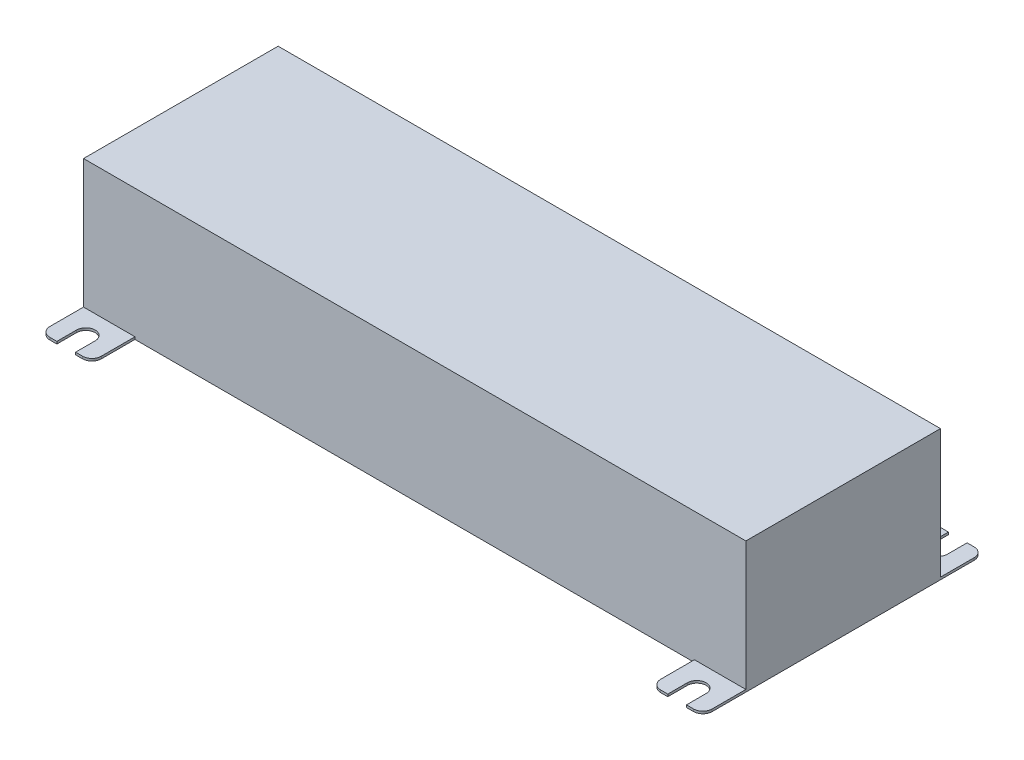
SolidWorks part; units mm, degrees
material "201.0-T43, per stampo in conchiglia (SS)"
ref_plane "Front Plane" through (0, 0, 0) normal (0, 0, 1) x (1, 0, 0)
ref_plane "Top Plane" through (0, 0, 0) normal (0, 1, 0) x (1, 0, 0)
ref_plane "Right Plane" through (0, 0, 0) normal (1, 0, 0) x (0, 0, -1)
sketch "Schizzo1" plane through (0, 0, 0) normal (0, 1, 0) x (1, 0, 0)
  line L0 (-70.8, 20.8) -> (70.8, -20.8) construction
  line L1 (-70.8, 20.8) -> (70.8, 20.8)
  line L2 (-70.8, 20.8) -> (-70.8, -20.8)
  line L3 (-70.8, -20.8) -> (70.8, -20.8)
  line L4 (70.8, 20.8) -> (70.8, -20.8)
  line L5 (-70.8, 0) -> (70.8, 0) construction
  point P4 (0, 0)
  dimension "D1" = 141.6
  dimension "D2" = 41.6
extrude "Estrusione-Estrusione1" add sketch "Schizzo1" along normal blind 28
sketch "Schizzo2" plane through (0, 0, 0) normal (0, 1, 0) x (1, 0, 0)
  line L0 (-70.8, 20.8) -> (-70.8, 28)
  line L1 (-68.8, 30) -> (-67.3, 30)
  line L2 (-67.3, 30) -> (-67.3, 25.8)
  line L3 (-59.8, 28) -> (-59.8, 20.8)
  line L4 (70.8, 20.8) -> (-70.8, 20.8) construction
  line L5 (-59.8, 20.8) -> (-70.8, 20.8)
  line L6 (-63.3, 25.8) -> (-63.3, 30)
  line L7 (-63.3, 30) -> (-61.8, 30)
  line L8 (-65.3, 20.8) -> (-65.3, 31.1814) construction
  line L9 (-70.8, 0) -> (0, 0) construction
  line L10 (-63.3, -30) -> (-61.8, -30)
  line L11 (-63.3, -25.8) -> (-63.3, -30)
  line L12 (-67.3, -30) -> (-67.3, -25.8)
  line L13 (-68.8, -30) -> (-67.3, -30)
  line L14 (-70.8, -20.8) -> (-70.8, -28)
  line L15 (-59.8, -20.8) -> (-70.8, -20.8)
  line L16 (-59.8, -28) -> (-59.8, -20.8)
  line L17 (0, 20.8) -> (0, -20.8) construction
  line L18 (-70.8, 20.8) -> (70.8, 20.8) construction
  line L19 (-70.8, -20.8) -> (70.8, -20.8) construction
  line L20 (63.3, -30) -> (61.8, -30)
  line L21 (63.3, -25.8) -> (63.3, -30)
  line L22 (67.3, -30) -> (67.3, -25.8)
  line L23 (68.8, -30) -> (67.3, -30)
  line L24 (70.8, -20.8) -> (70.8, -28)
  line L25 (59.8, -20.8) -> (70.8, -20.8)
  line L26 (59.8, -28) -> (59.8, -20.8)
  line L27 (63.3, 30) -> (61.8, 30)
  line L28 (63.3, 25.8) -> (63.3, 30)
  line L29 (67.3, 30) -> (67.3, 25.8)
  line L30 (68.8, 30) -> (67.3, 30)
  line L31 (70.8, 20.8) -> (70.8, 28)
  line L32 (59.8, 20.8) -> (70.8, 20.8)
  line L33 (59.8, 28) -> (59.8, 20.8)
  arc A0 (-70.8, 28) -> (-68.8, 30) centre (-68.8, 28) cw
  arc A1 (-67.3, 25.8) -> (-63.3, 25.8) centre (-65.3, 25.8) ccw
  arc A2 (-61.8, 30) -> (-59.8, 28) centre (-61.8, 28) cw
  arc A3 (-61.8, -30) -> (-59.8, -28) centre (-61.8, -28) ccw
  arc A4 (-67.3, -25.8) -> (-63.3, -25.8) centre (-65.3, -25.8) cw
  arc A5 (-70.8, -28) -> (-68.8, -30) centre (-68.8, -28) ccw
  arc A6 (61.8, -30) -> (59.8, -28) centre (61.8, -28) cw
  arc A7 (67.3, -25.8) -> (63.3, -25.8) centre (65.3, -25.8) ccw
  arc A8 (70.8, -28) -> (68.8, -30) centre (68.8, -28) cw
  arc A9 (61.8, 30) -> (59.8, 28) centre (61.8, 28) ccw
  arc A10 (67.3, 25.8) -> (63.3, 25.8) centre (65.3, 25.8) cw
  arc A11 (70.8, 28) -> (68.8, 30) centre (68.8, 28) ccw
  dimension "D1" = 2
  dimension "D2" = 2
  dimension "D5" = 2
  dimension "D7" = 11
  dimension "D4" = 130.6
  dimension "D3" = 2
  dimension "D6" = 4
  dimension "D8" = 51.6
  dimension "D9" = 60
extrude "Estrusione-Estrusione2" add sketch "Schizzo2" along normal blind 0.5
